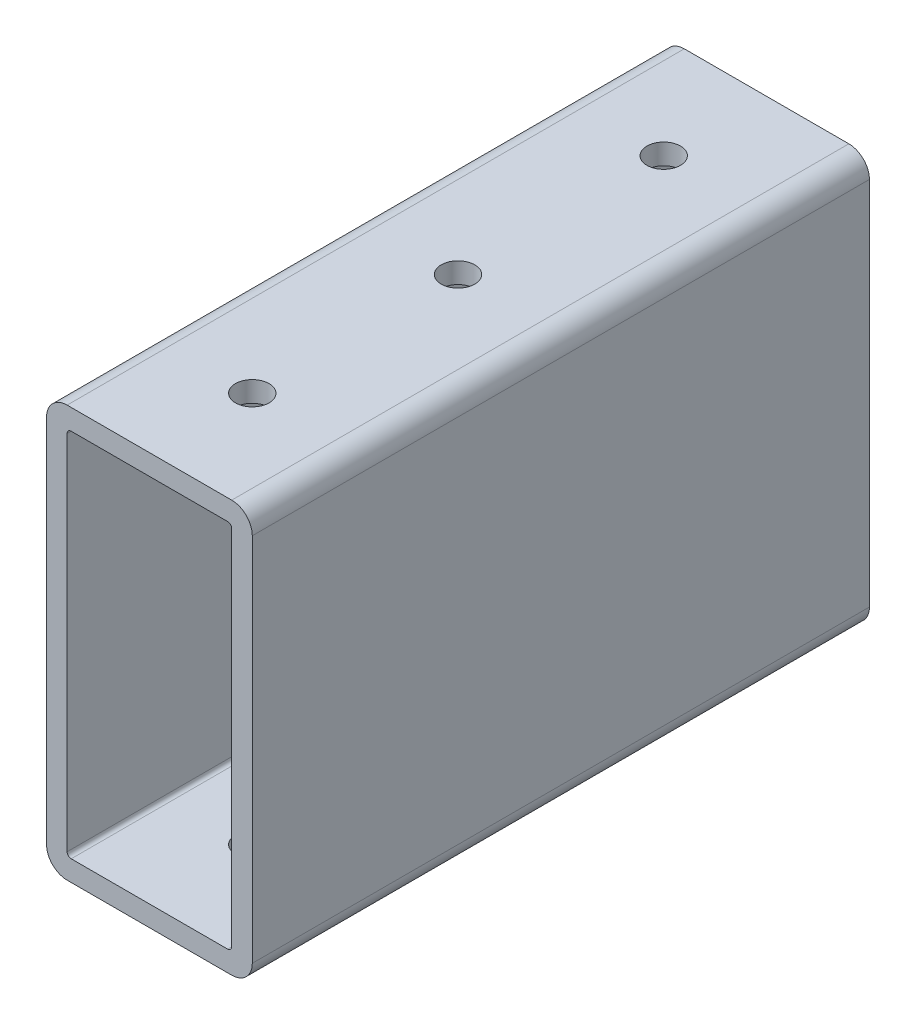
SolidWorks part; units mm, degrees
ref_plane "Front Plane" through (0, 0, 0) normal (0, 0, 1) x (1, 0, 0)
ref_plane "Top Plane" through (0, 0, 0) normal (0, 1, 0) x (1, 0, 0)
ref_plane "Right Plane" through (0, 0, 0) normal (1, 0, 0) x (0, 0, -1)
ref_plane "Plane1" through (12.7, 0, 0) normal (1, 0, 0) x (0, 0, -1)
sketch "Sketch1" plane through (12.7, 0, 0) normal (1, 0, 0) x (0, 0, -1)
  line L0 (38.1, -25.4) -> (38.1, 25.4)
  line L1 (38.1, 25.4) -> (-38.1, 25.4)
  line L2 (-38.1, 25.4) -> (-38.1, -25.4)
  line L3 (-38.1, -25.4) -> (38.1, -25.4)
  point P5 (0, 25.4)
  dimension "D1" = 50.8
  dimension "D2" = 25.4
  dimension "D3" = 76.2
extrude "Boss-Extrude1" add sketch "Sketch1" against normal blind 25.4
sketch "Sketch2" plane through (0, 0, -38.1) normal (0, 0, -1) x (-1, 0, 0)
  line L0 (10.16, -22.86) -> (10.16, 22.86)
  line L1 (10.16, 22.86) -> (-10.16, 22.86)
  line L2 (-10.16, 22.86) -> (-10.16, -22.86)
  line L3 (-10.16, -22.86) -> (10.16, -22.86)
extrude "Cut-Extrude1" cut sketch "Sketch2" against normal through all
hole_wizard "#6 Clearance Hole1" positions "Sketch4" profile "Sketch3" hole size "#6" standard "ANSI Inch"
sketch "Sketch4" plane through (0, -25.4, 0) normal (0, -1, 0) x (-1, 0, 0)
  point P0 (0, 711.2)
  point P1 (0, 736.6)
  point P2 (0, 685.8)
  point P3 (0, 660.4)
  point P4 (0, 635)
  point P5 (0, 609.6)
  point P6 (0, 584.2)
  point P7 (0, 558.8)
  point P8 (0, 533.4)
  point P9 (0, 508)
  point P10 (0, 482.6)
  point P11 (0, 457.2)
  point P12 (0, 431.8)
  point P13 (0, 406.4)
  point P14 (0, 381)
  point P15 (0, 355.6)
  point P16 (0, 330.2)
  point P17 (0, 304.8)
  point P18 (0, 279.4)
  point P19 (0, 254)
  point P20 (0, 228.6)
  point P21 (0, 203.2)
  point P22 (0, 177.8)
  point P23 (0, 152.4)
  point P24 (0, 127)
  point P25 (0, 101.6)
  point P26 (0, 76.2)
  point P27 (0, 50.8)
  point P28 (0, 25.4)
  point P29 (0, 0)
  point P30 (0, -25.4)
  point P31 (0, -50.8)
  point P32 (0, -76.2)
  point P33 (0, -101.6)
  point P34 (0, -127)
  point P35 (0, -152.4)
  point P36 (0, -177.8)
  point P37 (0, -203.2)
  point P38 (0, -228.6)
  point P39 (0, -254)
  point P40 (0, -279.4)
  point P41 (0, -304.8)
  point P42 (0, -330.2)
  point P43 (0, -355.6)
  point P44 (0, -381)
  point P45 (0, -406.4)
  point P46 (0, -431.8)
  point P47 (0, -457.2)
  point P48 (0, -482.6)
  point P49 (0, -508)
  point P50 (0, -533.4)
  point P51 (0, -558.8)
  point P52 (0, -584.2)
  point P53 (0, -609.6)
  point P54 (0, -635)
  point P55 (0, -660.4)
  point P56 (0, -685.8)
  point P57 (0, -711.2)
  point P58 (0, -736.6)
sketch "Sketch3" plane through (0, -25.4, -711.2) normal (1, 0, 0) x (0, 0, -1)
  line L0 (0, 0) -> (0, 50.8)
  line L1 (0, 50.8) -> (2.0701, 50.8)
  line L2 (2.0701, 50.8) -> (2.0701, 0)
  line L5 (2.0701, 0) -> (0, 0)
  line L11 (0, -6.35) -> (0, 107.95) construction
  dimension "Thru Hole Dia." = 4.1402
  dimension "Thru Hole Depth" = 50.8
hole_wizard "#6 Clearance Hole2" positions "Sketch6" profile "Sketch5" hole size "#6" standard "ANSI Inch"
sketch "Sketch6" plane through (0, 25.4, 0) normal (0, 1, 0) x (1, 0, 0)
  point P0 (0, 711.2)
  point P1 (0, 736.6)
  point P2 (0, 685.8)
  point P3 (0, 660.4)
  point P4 (0, 635)
  point P5 (0, 609.6)
  point P6 (0, 584.2)
  point P7 (0, 558.8)
  point P8 (0, 533.4)
  point P9 (0, 508)
  point P10 (0, 482.6)
  point P11 (0, 457.2)
  point P12 (0, 431.8)
  point P13 (0, 406.4)
  point P14 (0, 381)
  point P15 (0, 355.6)
  point P16 (0, 330.2)
  point P17 (0, 304.8)
  point P18 (0, 279.4)
  point P19 (0, 254)
  point P20 (0, 228.6)
  point P21 (0, 203.2)
  point P22 (0, 177.8)
  point P23 (0, 152.4)
  point P24 (0, 127)
  point P25 (0, 101.6)
  point P26 (0, 76.2)
  point P27 (0, 50.8)
  point P28 (0, 25.4)
  point P29 (0, 0)
  point P30 (0, -25.4)
  point P31 (0, -50.8)
  point P32 (0, -76.2)
  point P33 (0, -101.6)
  point P34 (0, -127)
  point P35 (0, -152.4)
  point P36 (0, -177.8)
  point P37 (0, -203.2)
  point P38 (0, -228.6)
  point P39 (0, -254)
  point P40 (0, -279.4)
  point P41 (0, -304.8)
  point P42 (0, -330.2)
  point P43 (0, -355.6)
  point P44 (0, -381)
  point P45 (0, -406.4)
  point P46 (0, -431.8)
  point P47 (0, -457.2)
  point P48 (0, -482.6)
  point P49 (0, -508)
  point P50 (0, -533.4)
  point P51 (0, -558.8)
  point P52 (0, -584.2)
  point P53 (0, -609.6)
  point P54 (0, -635)
  point P55 (0, -660.4)
  point P56 (0, -685.8)
  point P57 (0, -711.2)
  point P58 (0, -736.6)
sketch "Sketch5" plane through (0, 25.4, -711.2) normal (1, 0, 0) x (0, 0, 1)
  line L0 (0, 0) -> (0, 50.8)
  line L1 (0, 50.8) -> (2.0701, 50.8)
  line L2 (2.0701, 50.8) -> (2.0701, 0)
  line L5 (2.0701, 0) -> (0, 0)
  line L11 (0, -6.35) -> (0, 107.95) construction
  dimension "Thru Hole Dia." = 4.1402
  dimension "Thru Hole Depth" = 50.8
fillet "Fillet1" radius 0.5 4 edges at (10.16, 22.86, 0) (-10.16, -22.86, 0) (-10.16, 22.86, 0) (10.16, -22.86, 0)
fillet "Fillet2" radius 2.54 4 edges at (12.7, 25.4, 0) (-12.7, -25.4, 0) (12.7, -25.4, 0) (-12.7, 25.4, 0)
